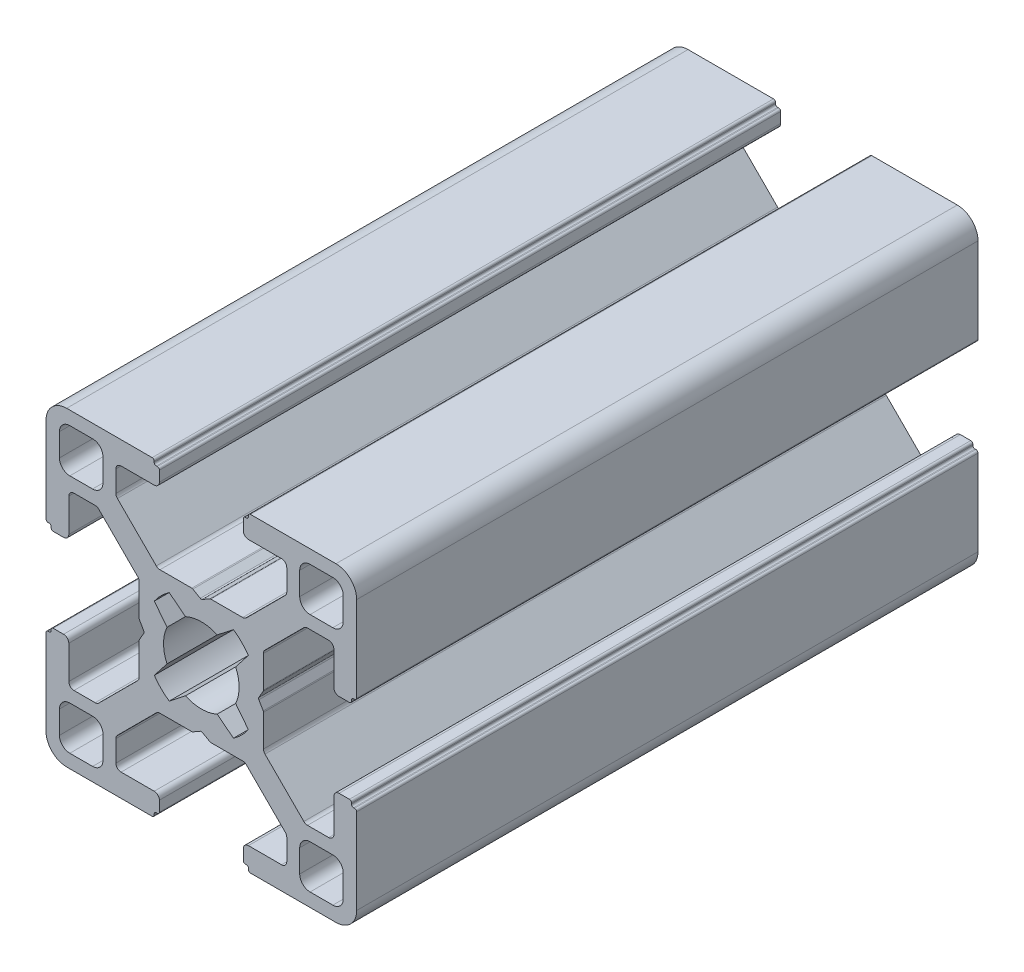
SolidWorks part; units mm, degrees
material "1060 Сплав"
ref_plane "Спереди" through (0, 0, 0) normal (0, 0, 1) x (1, 0, 0)
ref_plane "Сверху" through (0, 0, 0) normal (0, 1, 0) x (1, 0, 0)
ref_plane "Справа" through (0, 0, 0) normal (1, 0, 0) x (0, 0, -1)
sketch "Эскиз1" plane through (0, 0, 0) normal (0, 0, 1) x (1, 0, 0)
  line L0 (-5.5577, 0.1) -> (-5.9732, 0.8196)
  line L2 (-4.541, 3.1031) -> (-3.3131, 1.5316)
  line L3 (3.9968, 6) -> (0.9196, 6)
  line L4 (14.3, -4.05) -> (13.3, -4.05)
  line L5 (-3.1031, 4.541) -> (-1.5316, 3.3131)
  line L6 (4.541, -3.1031) -> (3.3131, -1.5316)
  line L7 (3.1031, 4.541) -> (1.5316, 3.3131)
  line L8 (-14.3, 4.05) -> (-13.3, 4.05)
  line L9 (-15, 4.75) -> (-15, 13)
  line L10 (-14.8, 4.55) -> (-14.7, 4.55)
  line L11 (-14.5, 4.35) -> (-14.5, 4.25)
  line L12 (-12.8, 4.55) -> (-12.8, 7.75)
  line L13 (-13.7, 12.7) -> (-13.7, 10.5)
  line L14 (-12.7, 13.7) -> (-10.5, 13.7)
  line L15 (-12.7, 9.5) -> (-10.5, 9.5)
  line L16 (-9.5, 10.5) -> (-9.5, 12.7)
  line L17 (-6, 0.9196) -> (-6, 3.9968)
  line L18 (-12.3, 8.25) -> (-10.2532, 8.25)
  line L19 (-6.1464, 4.3504) -> (-9.8996, 8.1036)
  line L20 (-5.5577, -0.1) -> (-5.9732, -0.8196)
  line L21 (-0.1, -5.5577) -> (-0.8196, -5.9732)
  line L22 (-6, -3.9968) -> (-6, -0.9196)
  line L23 (-4.3504, 6.1464) -> (-8.1036, 9.8996)
  line L24 (-0.9196, -6) -> (-3.9968, -6)
  line L25 (4.541, 3.1031) -> (3.3131, 1.5316)
  line L26 (3.1031, -4.541) -> (1.5316, -3.3131)
  line L27 (-3.1031, -4.541) -> (-1.5316, -3.3131)
  line L28 (-4.541, -3.1031) -> (-3.3131, -1.5316)
  line L29 (0.1, -5.5577) -> (0.8196, -5.9732)
  line L36 (-8.25, 12.3) -> (-8.25, 10.2532)
  line L37 (-0.9196, 6) -> (-3.9968, 6)
  line L38 (-4.55, 12.8) -> (-7.75, 12.8)
  line L39 (-4.35, 14.5) -> (-4.25, 14.5)
  line L40 (-4.55, 14.8) -> (-4.55, 14.7)
  line L41 (-4.75, 15) -> (-13, 15)
  line L42 (-4.05, 14.3) -> (-4.05, 13.3)
  line L43 (0.1, 5.5577) -> (0.8196, 5.9732)
  line L44 (-0.9196, 6) -> (-3.9968, 6)
  line L45 (-0.1, 5.5577) -> (-0.8196, 5.9732)
  line L46 (-4.05, -14.3) -> (-4.05, -13.3)
  line L47 (-4.75, -15) -> (-13, -15)
  line L48 (-4.55, -14.8) -> (-4.55, -14.7)
  line L49 (-4.35, -14.5) -> (-4.25, -14.5)
  line L50 (-4.55, -12.8) -> (-7.75, -12.8)
  line L51 (-8.25, -12.3) -> (-8.25, -10.2532)
  line L52 (-4.3504, -6.1464) -> (-8.1036, -9.8996)
  line L53 (-6.1464, -4.3504) -> (-9.8996, -8.1036)
  line L54 (-12.3, -8.25) -> (-10.2532, -8.25)
  line L55 (-9.5, -10.5) -> (-9.5, -12.7)
  line L56 (-12.7, -9.5) -> (-10.5, -9.5)
  line L57 (-12.7, -13.7) -> (-10.5, -13.7)
  line L58 (-13.7, -12.7) -> (-13.7, -10.5)
  line L59 (-12.8, -4.55) -> (-12.8, -7.75)
  line L60 (-14.5, -4.35) -> (-14.5, -4.25)
  line L61 (-14.8, -4.55) -> (-14.7, -4.55)
  line L62 (-15, -4.75) -> (-15, -13)
  line L63 (-14.3, -4.05) -> (-13.3, -4.05)
  line L64 (15, -4.75) -> (15, -13)
  line L65 (14.8, -4.55) -> (14.7, -4.55)
  line L66 (14.5, -4.35) -> (14.5, -4.25)
  line L67 (12.8, -4.55) -> (12.8, -7.75)
  line L68 (13.7, -12.7) -> (13.7, -10.5)
  line L69 (12.7, -13.7) -> (10.5, -13.7)
  line L70 (12.7, -9.5) -> (10.5, -9.5)
  line L71 (9.5, -10.5) -> (9.5, -12.7)
  line L72 (12.3, -8.25) -> (10.2532, -8.25)
  line L73 (6.1464, -4.3504) -> (9.8996, -8.1036)
  line L74 (4.3504, -6.1464) -> (8.1036, -9.8996)
  line L75 (8.25, -12.3) -> (8.25, -10.2532)
  line L76 (4.55, -12.8) -> (7.75, -12.8)
  line L77 (4.35, -14.5) -> (4.25, -14.5)
  line L78 (4.55, -14.8) -> (4.55, -14.7)
  line L79 (4.75, -15) -> (13, -15)
  line L80 (4.05, -14.3) -> (4.05, -13.3)
  line L81 (4.05, 14.3) -> (4.05, 13.3)
  line L82 (4.75, 15) -> (13, 15)
  line L83 (4.55, 14.8) -> (4.55, 14.7)
  line L84 (4.35, 14.5) -> (4.25, 14.5)
  line L85 (4.55, 12.8) -> (7.75, 12.8)
  line L86 (8.25, 12.3) -> (8.25, 10.2532)
  line L89 (4.3504, 6.1464) -> (8.1036, 9.8996)
  line L90 (6, -3.9968) -> (6, -0.9196)
  line L91 (5.5577, -0.1) -> (5.9732, -0.8196)
  line L92 (6.1464, 4.3504) -> (9.8996, 8.1036)
  line L93 (12.3, 8.25) -> (10.2532, 8.25)
  line L94 (6, 0.9196) -> (6, 3.9968)
  line L95 (9.5, 10.5) -> (9.5, 12.7)
  line L96 (12.7, 9.5) -> (10.5, 9.5)
  line L97 (12.7, 13.7) -> (10.5, 13.7)
  line L98 (13.7, 12.7) -> (13.7, 10.5)
  line L99 (12.8, 4.55) -> (12.8, 7.75)
  line L100 (14.5, 4.35) -> (14.5, 4.25)
  line L101 (14.8, 4.55) -> (14.7, 4.55)
  line L102 (15, 4.75) -> (15, 13)
  line L103 (14.3, 4.05) -> (13.3, 4.05)
  line L104 (5.5577, 0.1) -> (5.9732, 0.8196)
  line L105 (-0.9196, -6) -> (-3.9968, -6)
  line L106 (3.9968, -6) -> (0.9196, -6)
  arc A0 (-13, 15) -> (-15, 13) centre (-13, 13) ccw
  arc A1 (-10.5, 13.7) -> (-9.5, 12.7) centre (-10.5, 12.7) cw
  arc A2 (-10.5, 9.5) -> (-9.5, 10.5) centre (-10.5, 10.5) ccw
  arc A3 (-13.7, 10.5) -> (-12.7, 9.5) centre (-12.7, 10.5) ccw
  arc A4 (-13.7, 12.7) -> (-12.7, 13.7) centre (-12.7, 12.7) cw
  arc A5 (-3.3624, 1.42) -> (-3.3624, -1.42) centre (0, 0) ccw
  arc A6 (-4.541, -3.1031) -> (-3.1031, -4.541) centre (0, 0) ccw
  arc A7 (-1.42, -3.3624) -> (1.42, -3.3624) centre (0, 0) ccw
  arc A8 (3.1031, -4.541) -> (4.541, -3.1031) centre (0, 0) ccw
  arc A9 (3.3624, -1.42) -> (3.3624, 1.42) centre (0, 0) ccw
  arc A10 (4.541, 3.1031) -> (3.1031, 4.541) centre (0, 0) ccw
  arc A11 (1.42, 3.3624) -> (-1.42, 3.3624) centre (0, 0) ccw
  arc A12 (-3.1031, 4.541) -> (-4.541, 3.1031) centre (0, 0) ccw
  arc A13 (-14.5, 4.25) -> (-14.3, 4.05) centre (-14.3, 4.25) ccw
  arc A14 (-14.7, 4.55) -> (-14.5, 4.35) centre (-14.7, 4.35) cw
  arc A15 (-14.8, 4.55) -> (-15, 4.75) centre (-14.8, 4.75) cw
  arc A16 (-13.3, 4.05) -> (-12.8, 4.55) centre (-13.3, 4.55) ccw
  arc A17 (-6.1464, 4.3504) -> (-6, 3.9968) centre (-6.5, 3.9968) cw
  arc A18 (-9.8996, 8.1036) -> (-10.2532, 8.25) centre (-10.2532, 7.75) ccw
  arc A19 (-12.8, 7.75) -> (-12.3, 8.25) centre (-12.3, 7.75) cw
  arc A20 (-5.9732, 0.8196) -> (-6, 0.9196) centre (-5.8, 0.9196) cw
  arc A21 (-5.5577, -0.1) -> (-5.5577, 0.1) centre (-5.7309, 0) ccw
  arc A22 (-5.9732, -0.8196) -> (-6, -0.9196) centre (-5.8, -0.9196) ccw
  arc A23 (-7.75, 12.8) -> (-8.25, 12.3) centre (-7.75, 12.3) ccw
  arc A24 (-8.1036, 9.8996) -> (-8.25, 10.2532) centre (-7.75, 10.2532) cw
  arc A25 (-4.3504, 6.1464) -> (-3.9968, 6) centre (-3.9968, 6.5) ccw
  arc A26 (-4.05, 13.3) -> (-4.55, 12.8) centre (-4.55, 13.3) cw
  arc A27 (-4.55, 14.8) -> (-4.75, 15) centre (-4.75, 14.8) ccw
  arc A28 (-4.55, 14.7) -> (-4.35, 14.5) centre (-4.35, 14.7) ccw
  arc A29 (-4.25, 14.5) -> (-4.05, 14.3) centre (-4.25, 14.3) cw
  arc A30 (0.8196, 5.9732) -> (0.9196, 6) centre (0.9196, 5.8) cw
  arc A31 (0.1, 5.5577) -> (-0.1, 5.5577) centre (0, 5.7309) cw
  arc A32 (-0.8196, 5.9732) -> (-0.9196, 6) centre (-0.9196, 5.8) ccw
  arc A33 (-4.25, -14.5) -> (-4.05, -14.3) centre (-4.25, -14.3) ccw
  arc A34 (-4.55, -14.7) -> (-4.35, -14.5) centre (-4.35, -14.7) cw
  arc A35 (-4.55, -14.8) -> (-4.75, -15) centre (-4.75, -14.8) cw
  arc A36 (-4.05, -13.3) -> (-4.55, -12.8) centre (-4.55, -13.3) ccw
  arc A37 (-4.3504, -6.1464) -> (-3.9968, -6) centre (-3.9968, -6.5) cw
  arc A38 (-8.1036, -9.8996) -> (-8.25, -10.2532) centre (-7.75, -10.2532) ccw
  arc A39 (-7.75, -12.8) -> (-8.25, -12.3) centre (-7.75, -12.3) cw
  arc A40 (-12.8, -7.75) -> (-12.3, -8.25) centre (-12.3, -7.75) ccw
  arc A41 (-9.8996, -8.1036) -> (-10.2532, -8.25) centre (-10.2532, -7.75) cw
  arc A42 (-6.1464, -4.3504) -> (-6, -3.9968) centre (-6.5, -3.9968) ccw
  arc A43 (-13.3, -4.05) -> (-12.8, -4.55) centre (-13.3, -4.55) cw
  arc A44 (-14.8, -4.55) -> (-15, -4.75) centre (-14.8, -4.75) ccw
  arc A45 (-14.7, -4.55) -> (-14.5, -4.35) centre (-14.7, -4.35) ccw
  arc A46 (-14.5, -4.25) -> (-14.3, -4.05) centre (-14.3, -4.25) cw
  arc A47 (-13.7, -12.7) -> (-12.7, -13.7) centre (-12.7, -12.7) ccw
  arc A48 (-13.7, -10.5) -> (-12.7, -9.5) centre (-12.7, -10.5) cw
  arc A49 (-10.5, -9.5) -> (-9.5, -10.5) centre (-10.5, -10.5) cw
  arc A50 (-10.5, -13.7) -> (-9.5, -12.7) centre (-10.5, -12.7) ccw
  arc A51 (-13, -15) -> (-15, -13) centre (-13, -13) cw
  arc A52 (13, -15) -> (15, -13) centre (13, -13) ccw
  arc A53 (10.5, -13.7) -> (9.5, -12.7) centre (10.5, -12.7) cw
  arc A54 (10.5, -9.5) -> (9.5, -10.5) centre (10.5, -10.5) ccw
  arc A55 (13.7, -10.5) -> (12.7, -9.5) centre (12.7, -10.5) ccw
  arc A56 (13.7, -12.7) -> (12.7, -13.7) centre (12.7, -12.7) cw
  arc A57 (14.5, -4.25) -> (14.3, -4.05) centre (14.3, -4.25) ccw
  arc A58 (14.7, -4.55) -> (14.5, -4.35) centre (14.7, -4.35) cw
  arc A59 (14.8, -4.55) -> (15, -4.75) centre (14.8, -4.75) cw
  arc A60 (13.3, -4.05) -> (12.8, -4.55) centre (13.3, -4.55) ccw
  arc A61 (6.1464, -4.3504) -> (6, -3.9968) centre (6.5, -3.9968) cw
  arc A62 (9.8996, -8.1036) -> (10.2532, -8.25) centre (10.2532, -7.75) ccw
  arc A63 (12.8, -7.75) -> (12.3, -8.25) centre (12.3, -7.75) cw
  arc A64 (7.75, -12.8) -> (8.25, -12.3) centre (7.75, -12.3) ccw
  arc A65 (8.1036, -9.8996) -> (8.25, -10.2532) centre (7.75, -10.2532) cw
  arc A66 (4.3504, -6.1464) -> (3.9968, -6) centre (3.9968, -6.5) ccw
  arc A67 (4.05, -13.3) -> (4.55, -12.8) centre (4.55, -13.3) cw
  arc A68 (4.55, -14.8) -> (4.75, -15) centre (4.75, -14.8) ccw
  arc A69 (4.55, -14.7) -> (4.35, -14.5) centre (4.35, -14.7) ccw
  arc A70 (4.25, -14.5) -> (4.05, -14.3) centre (4.25, -14.3) cw
  arc A71 (4.25, 14.5) -> (4.05, 14.3) centre (4.25, 14.3) ccw
  arc A72 (4.55, 14.7) -> (4.35, 14.5) centre (4.35, 14.7) cw
  arc A73 (4.55, 14.8) -> (4.75, 15) centre (4.75, 14.8) cw
  arc A74 (4.05, 13.3) -> (4.55, 12.8) centre (4.55, 13.3) ccw
  arc A75 (4.3504, 6.1464) -> (3.9968, 6) centre (3.9968, 6.5) cw
  arc A76 (8.1036, 9.8996) -> (8.25, 10.2532) centre (7.75, 10.2532) ccw
  arc A77 (7.75, 12.8) -> (8.25, 12.3) centre (7.75, 12.3) cw
  arc A78 (5.9732, -0.8196) -> (6, -0.9196) centre (5.8, -0.9196) cw
  arc A79 (5.5577, -0.1) -> (5.5577, 0.1) centre (5.7309, 0) cw
  arc A80 (5.9732, 0.8196) -> (6, 0.9196) centre (5.8, 0.9196) ccw
  arc A81 (12.8, 7.75) -> (12.3, 8.25) centre (12.3, 7.75) ccw
  arc A82 (9.8996, 8.1036) -> (10.2532, 8.25) centre (10.2532, 7.75) cw
  arc A83 (6.1464, 4.3504) -> (6, 3.9968) centre (6.5, 3.9968) ccw
  arc A84 (13.3, 4.05) -> (12.8, 4.55) centre (13.3, 4.55) cw
  arc A85 (14.8, 4.55) -> (15, 4.75) centre (14.8, 4.75) ccw
  arc A86 (14.7, 4.55) -> (14.5, 4.35) centre (14.7, 4.35) ccw
  arc A87 (14.5, 4.25) -> (14.3, 4.05) centre (14.3, 4.25) cw
  arc A88 (3.1031, 4.541) -> (4.541, 3.1031) centre (0, 0) cw
  arc A89 (4.541, -3.1031) -> (3.1031, -4.541) centre (0, 0) cw
  arc A90 (3.3624, 1.42) -> (3.3624, -1.42) centre (0, 0) cw
  arc A91 (13.7, 12.7) -> (12.7, 13.7) centre (12.7, 12.7) ccw
  arc A92 (13.7, 10.5) -> (12.7, 9.5) centre (12.7, 10.5) cw
  arc A93 (10.5, 9.5) -> (9.5, 10.5) centre (10.5, 10.5) cw
  arc A94 (10.5, 13.7) -> (9.5, 12.7) centre (10.5, 12.7) ccw
  arc A95 (13, 15) -> (15, 13) centre (13, 13) cw
  arc A96 (-0.8196, -5.9732) -> (-0.9196, -6) centre (-0.9196, -5.8) cw
  arc A97 (0.1, -5.5577) -> (-0.1, -5.5577) centre (0, -5.7309) ccw
  arc A98 (0.8196, -5.9732) -> (0.9196, -6) centre (0.9196, -5.8) ccw
  arc A99 (-3.3131, 1.5316) -> (-3.3131, -1.5316) centre (0, 0) ccw
  arc A100 (3.3131, 1.5316) -> (3.3131, -1.5316) centre (0, 0) cw
  arc A101 (3.1031, 4.541) -> (4.541, 3.1031) centre (0, 0) cw
  arc A102 (3.1031, -4.541) -> (4.541, -3.1031) centre (0, 0) ccw
  arc A103 (3.1031, -4.541) -> (4.541, -3.1031) centre (0, 0) ccw
  arc A104 (-3.1031, -4.541) -> (-4.541, -3.1031) centre (0, 0) cw
  arc A105 (1.42, -3.3624) -> (-1.42, -3.3624) centre (0, 0) cw
  arc A106 (4.541, -3.1031) -> (3.1031, -4.541) centre (0, 0) cw
  arc A107 (3.3131, -1.5316) -> (3.3131, 1.5316) centre (0, 0) ccw
  arc A108 (1.5316, -3.3131) -> (-1.5316, -3.3131) centre (0, 0) cw
  arc A109 (1.5316, 3.3131) -> (-1.5316, 3.3131) centre (0, 0) ccw
  arc A110 (-1.5316, 3.3131) -> (1.5316, 3.3131) centre (0, 0) cw
  arc A111 (-1.5316, -3.3131) -> (1.5316, -3.3131) centre (0, 0) ccw
  arc A112 (-3.3131, -1.5316) -> (-3.3131, 1.5316) centre (0, 0) cw
  point P26 (-9.5, 9.5)
  point P43 (-3.8891, 3.8891)
  point P63 (-15, 4.55)
  point P74 (-6, 0.866)
  point P101 (-4.55, 15)
  point P110 (-0.866, 6)
  point P168 (-4.55, -15)
  point P169 (-15, -4.55)
  point P170 (-3.8891, -3.8891)
  point P171 (-9.5, -9.5)
  point P294 (9.5, -9.5)
  point P295 (3.8891, -3.8891)
  point P296 (15, -4.55)
  point P297 (4.55, -15)
  point P298 (4.55, 15)
  point P299 (6, 0.866)
  point P300 (15, 4.55)
  point P301 (3.8891, 3.8891)
  point P302 (9.5, 9.5)
  point P311 (-0.866, -6)
extrude "Бобышка-Вытянуть1" add sketch "Эскиз1" along normal blind 60 contours L29 A98 L106 A66 L74 A65 L75 A64 L76 A67 L80 A70 L77 A69 L78 A68 L79 A52 L64 A59 L65 A58 L66 A57 L4 A60 L67 A63 L72 A62 L73 A61 L90 A78 L91 A79 L104 A80 L94 A83 L92 A82 L93 A81 L99 A84 L103 A87 L100 A86 L101
